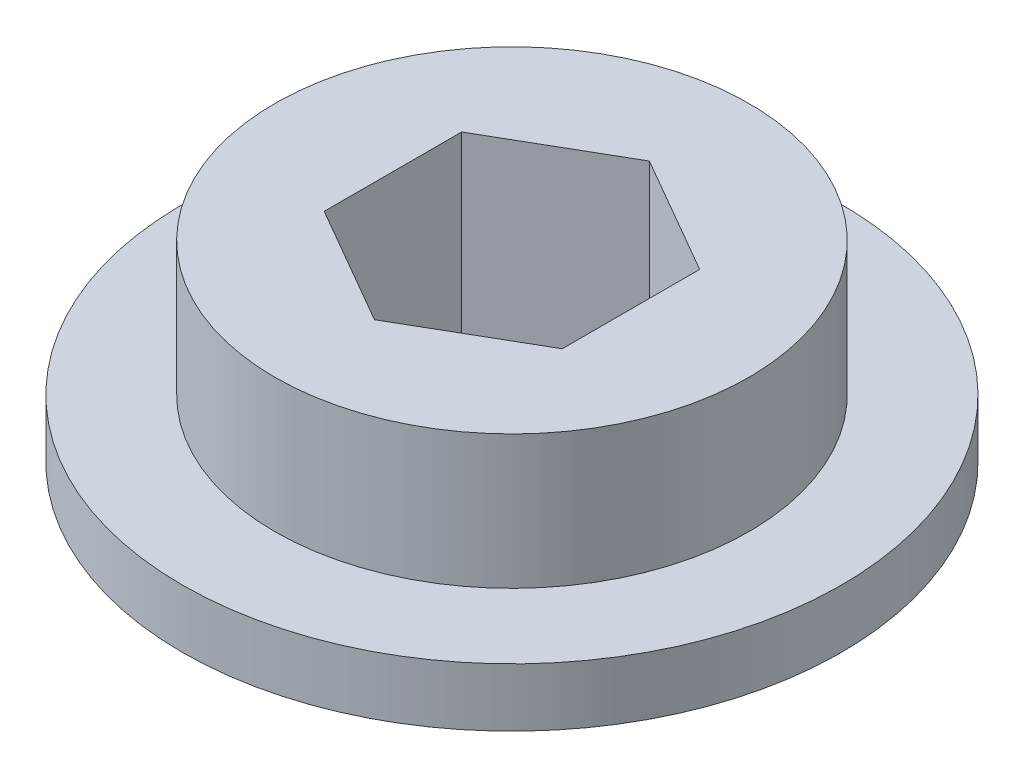
SolidWorks part; units mm, degrees
ref_plane "Front Plane" through (0, 0, 0) normal (0, 0, 1) x (1, 0, 0)
ref_plane "Top Plane" through (0, 0, 0) normal (0, 1, 0) x (1, 0, 0)
ref_plane "Right Plane" through (0, 0, 0) normal (1, 0, 0) x (0, 0, -1)
sketch "Sketch1" plane through (0, 0, 0) normal (0, 1, 0) x (1, 0, 0)
  line L0 (0, 0) -> (0, 7.3617) construction
  line L1 (0, 7.3617) -> (-6.3754, 3.6808)
  line L2 (-6.3754, 3.6808) -> (-6.3754, -3.6808)
  line L3 (-6.3754, -3.6808) -> (0, -7.3617)
  line L4 (0, -7.3617) -> (6.3754, -3.6808)
  line L5 (6.3754, -3.6808) -> (6.3754, 3.6808)
  line L6 (6.3754, 3.6808) -> (0, 7.3617)
  circle A0 centre (0, 0) radius 17.653
  circle A1 centre (0, 0) radius 6.3754 construction
  dimension "D1" = 35.306
  dimension "D2" = 12.7508
extrude "Boss-Extrude1" add sketch "Sketch1" along normal blind 10.287 contours A0 | L4 L5 L6 L1 L2 L3
sketch "Sketch2" plane through (0, 0, 0) normal (0, 1, 0) x (1, 0, 0)
  circle A0 centre (0, 0) radius 16.383
  dimension "D1" = 32.766
sketch "Sketch3" plane through (0, 10.287, 0) normal (0, 1, 0) x (1, 0, 0)
  circle A0 centre (0, 0) radius 12.7
  circle A1 centre (0, 0) radius 23.749
  dimension "D1" = 25.4
extrude "Cut-Extrude2" cut sketch "Sketch3" against normal blind 7.1628
